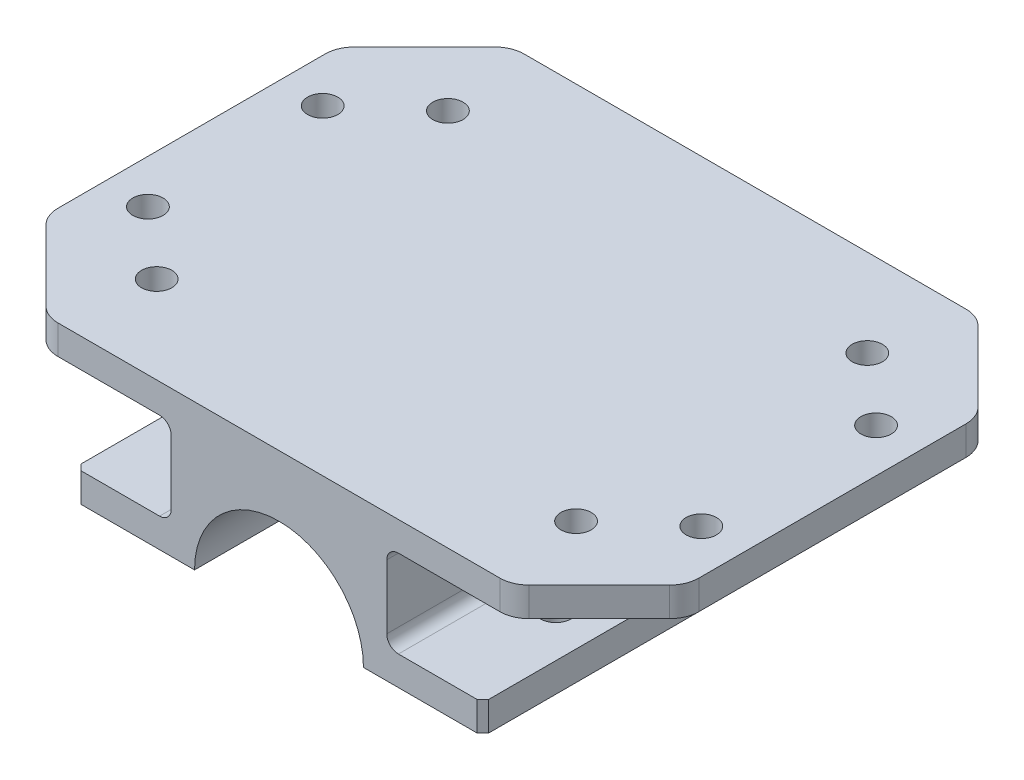
SolidWorks part; units mm, degrees
ref_plane "前视基准面" through (0, 0, 0) normal (0, 0, 1) x (1, 0, 0)
ref_plane "上视基准面" through (0, 0, 0) normal (0, 1, 0) x (1, 0, 0)
ref_plane "右视基准面" through (0, 0, 0) normal (1, 0, 0) x (0, 0, -1)
sketch "草图2" plane through (0, 0, 0) normal (0, 0, 1) x (1, 0, 0)
  line L0 (25, 0) -> (14.5, 0)
  line L1 (-25, 0) -> (-35, 0)
  line L2 (-35, 0) -> (-35, 5)
  line L3 (-35, 25) -> (35, 25)
  line L4 (0, 25) -> (0, 14.5) construction
  line L5 (25, 0) -> (35, 0)
  line L6 (35, 0) -> (35, 5)
  line L7 (-14.5, 0) -> (-25, 0)
  line L8 (-35, 25) -> (-55, 25)
  line L9 (-55, 25) -> (-55, 20)
  line L10 (-55, 20) -> (-35, 20)
  line L12 (-35, 5) -> (-22.5, 5)
  line L13 (-22.5, 5) -> (-22.5, 20)
  line L14 (-22.5, 20) -> (-35, 20)
  line L15 (22.5, 5) -> (22.5, 20)
  line L16 (22.5, 20) -> (35, 20)
  line L17 (35, 5) -> (22.5, 5)
  line L18 (55, 20) -> (35, 20)
  line L19 (55, 25) -> (55, 20)
  line L20 (35, 25) -> (55, 25)
  arc A0 (14.5, 0) -> (-14.5, 0) centre (0, 0) ccw
  dimension "D1" = 5
  dimension "D7" = 14.5
  dimension "D2" = 5
  dimension "D3" = 20
  dimension "D4" = 35
  dimension "D5" = 15
  dimension "D6" = 22.5
  dimension "D8" = 35
extrude "凸台-拉伸2" add sketch "草图2" along normal mid plane 80
sketch "草图3" plane through (0, 20, 0) normal (0, -1, 0) x (1, 0, 0)
  line L0 (-55, 40) -> (-55, 20) construction
  line L1 (-55, 40) -> (-55, -40) construction
  line L2 (-55, 20) -> (-27.5, 20) construction
  line L3 (0, 0) -> (0, 10) construction
  line L4 (0, 0) -> (10, 0) construction
  circle A0 centre (-27.5, 20) radius 2.6
  circle A1 centre (27.5, 20) radius 2.6
  circle A2 centre (27.5, -20) radius 2.6
  circle A3 centre (-27.5, -20) radius 2.6
extrude "切除-拉伸2" cut sketch "草图3" along normal blind 20
chamfer "倒角2" distance 1 angle 45 4 edges at (-35, 2.5, 40) (35, 2.5, 40) (-35, 2.5, -40) (35, 2.5, -40)
sketch "草图4" plane through (0, 25, 0) normal (0, 1, 0) x (1, 0, 0)
  line L0 (55, 0) -> (55, -25) construction
  line L1 (55, -40) -> (55, 40) construction
  line L2 (55, -25) -> (36, -25) construction
  line L3 (0, 0) -> (0, -10) construction
  line L4 (0, 0) -> (10, 0) construction
  circle A0 centre (36, -25) radius 2.6
  circle A1 centre (-36, -25) radius 2.6
  circle A2 centre (36, 25) radius 2.6
  circle A3 centre (-36, 25) radius 2.6
  dimension "D1" = 36
  dimension "D2" = 25
  dimension "D3" = 5.2
extrude "切除-拉伸3" cut sketch "草图4" against normal blind 10
sketch "草图5" plane through (0, 25, 0) normal (0, 1, 0) x (1, 0, 0)
  line L1 (-47.5, -15) -> (47.5, -15) construction
  line L2 (-47.5, -15) -> (-47.5, 15) construction
  line L3 (-47.5, 15) -> (47.5, 15) construction
  line L4 (47.5, -15) -> (47.5, 15) construction
  line L5 (-47.5, -15) -> (47.5, 15) construction
  line L6 (-47.5, 15) -> (47.5, -15) construction
  circle A0 centre (-47.5, 15) radius 2.6
  circle A1 centre (47.5, 15) radius 2.6
  circle A2 centre (47.5, -15) radius 2.6
  circle A3 centre (-47.5, -15) radius 2.6
  point P0 (0, 0)
  dimension "D1" = 30
  dimension "D2" = 95
extrude "切除-拉伸4" cut sketch "草图5" against normal blind 10
chamfer "倒角3" distance 15 angle 45 4 edges at (55, 22.5, -40) (55, 22.5, 40) (-55, 22.5, -40) (-55, 22.5, 40)
fillet "圆角2" radius 5 8 edges at (-55, 22.5, -25) (-40, 22.5, -40) (40, 22.5, -40) (55, 22.5, -25) (55, 22.5, 25) (40, 22.5, 40) (-40, 22.5, 40) (-55, 22.5, 25)
sketch "Sketch1" plane through (0, 0, 40) normal (0, 0, 1) x (1, 0, 0)
  line L0 (-22.5, 20) -> (-22.5, 5)
  line L1 (-22.5, 5) -> (-18.5, 5)
  line L2 (-18.5, 5) -> (-18.5, 20)
  line L3 (-18.5, 20) -> (-22.5, 20)
  line L4 (0, 0) -> (0, 8.0636) construction
  line L5 (18.5, 5) -> (18.5, 20)
  line L6 (22.5, 5) -> (18.5, 5)
  line L7 (22.5, 20) -> (22.5, 5)
  line L8 (18.5, 20) -> (22.5, 20)
  dimension "D1" = 4
extrude "Cut-Extrude1" cut sketch "Sketch1" against normal through all
fillet "Fillet1" radius 2 4 edges at (18.5, 20, 0) (18.5, 5, 0) (-18.5, 20, 0) (-18.5, 5, 0)
